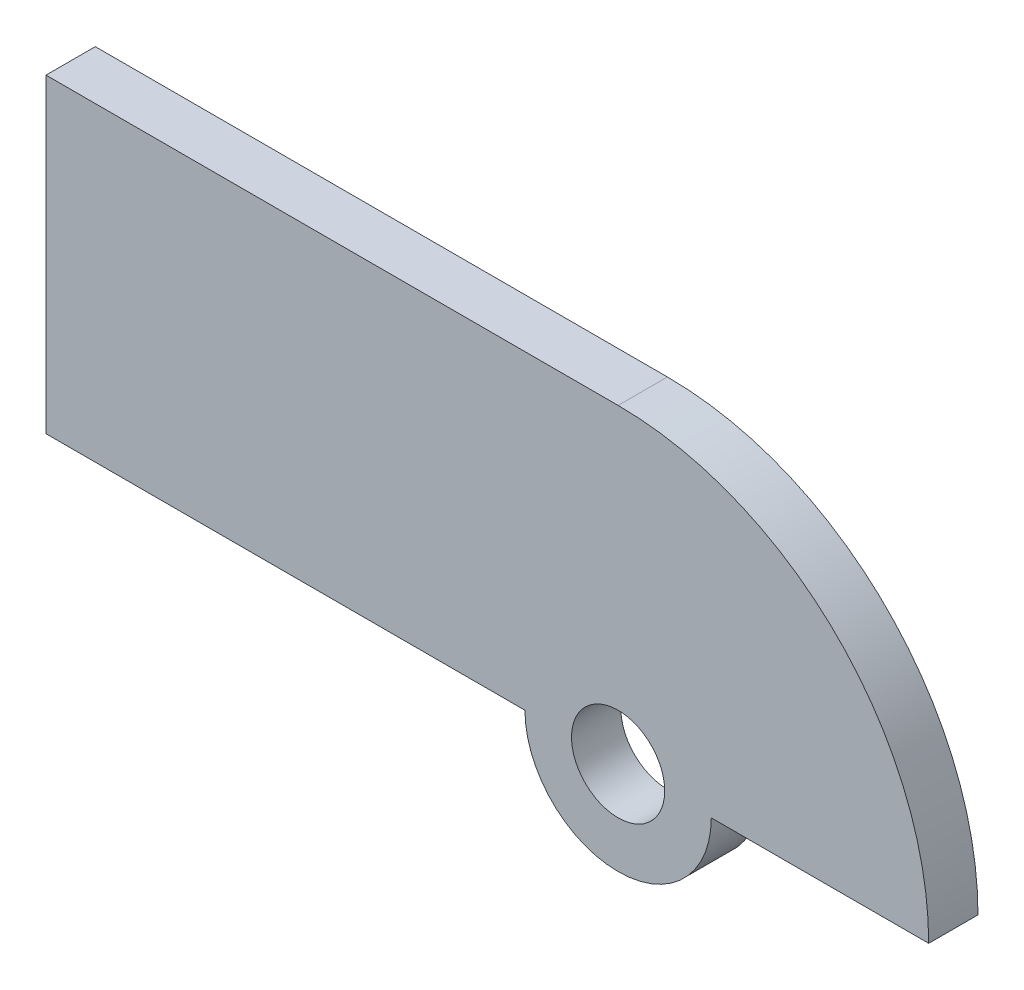
SolidWorks part; units mm, degrees
ref_plane "Front Plane" through (0, 0, 0) normal (0, 0, 1) x (1, 0, 0)
ref_plane "Top Plane" through (0, 0, 0) normal (0, 1, 0) x (1, 0, 0)
ref_plane "Right Plane" through (0, 0, 0) normal (1, 0, 0) x (0, 0, -1)
sketch "Sketch1" plane through (0, 0, 0) normal (0, 0, 1) x (1, 0, 0)
  line L0 (0, 0) -> (20, 0)
  line L1 (0, 0) -> (-36.8421, 0)
  line L2 (0, 0) -> (0, 20)
  line L3 (0, 20) -> (-36.8421, 20)
  line L4 (-36.8421, 0) -> (-36.8421, 20)
  circle A0 centre (0, 0) radius 3
  arc A1 (20, 0) -> (0, 20) centre (0, 0) ccw
  circle A2 centre (0, 0) radius 6
  dimension "D1" = 6
  dimension "D2" = 40
  dimension "D3" = 12
extrude "Boss-Extrude1" add sketch "Sketch1" along normal blind 3.175 contours A0 L2 L3 L4 L1 | A2 L0 A1 L2 | L1 A2 L0 A0 | L0 A2 L2 A0 | L2 A2 L1 A0
